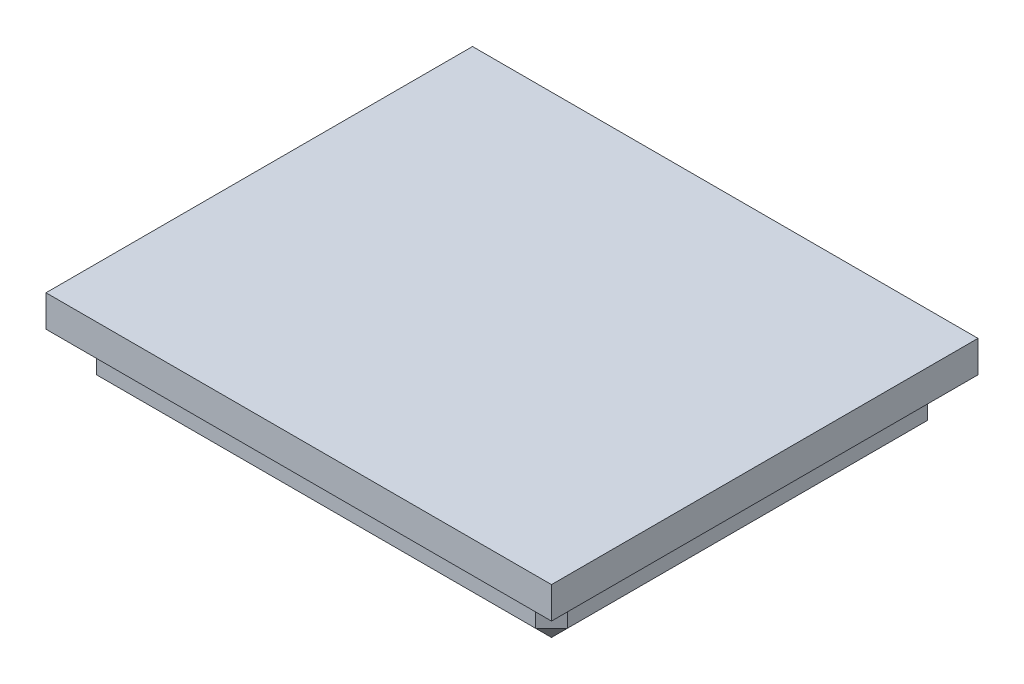
SolidWorks part; units mm, degrees
ref_plane "Спереди" through (0, 0, 0) normal (0, 0, 1) x (1, 0, 0)
ref_plane "Сверху" through (0, 0, 0) normal (0, 1, 0) x (1, 0, 0)
ref_plane "Справа" through (0, 0, 0) normal (1, 0, 0) x (0, 0, -1)
sketch "Sketch1" plane through (0, 0, 0) normal (0, 1, 0) x (1, 0, 0)
  line L1 (14.9, -12.4) -> (-14.9, -12.4)
  line L2 (14.9, -12.4) -> (14.9, 12.4)
  line L3 (14.9, 12.4) -> (-14.9, 12.4)
  line L4 (-14.9, -12.4) -> (-14.9, 12.4)
  line L5 (14.9, -12.4) -> (-14.9, 12.4) construction
  line L6 (14.9, 12.4) -> (-14.9, -12.4) construction
  point P0 (0, 0)
  dimension "D1" = 29.8
  dimension "D2" = 24.8
extrude "Boss-Extrude1" add sketch "Sketch1" along normal blind 3
sketch "Sketch2" plane through (0, 3, 0) normal (0, 1, 0) x (1, 0, 0)
  line L0 (-14.9, 12.4) -> (14.9, -12.4) construction
  line L1 (0, 13.5) -> (0, -13.5) construction
  line L2 (16, -13.5) -> (-16, -13.5)
  line L3 (16, -13.5) -> (16, 13.5)
  line L4 (16, 13.5) -> (-16, 13.5)
  line L5 (-16, -13.5) -> (-16, 13.5)
  line L6 (16, -13.5) -> (-16, 13.5) construction
  line L7 (16, 13.5) -> (-16, -13.5) construction
  point P4 (0, 0)
  dimension "D1" = 32
  dimension "D2" = 27
extrude "Boss-Extrude2" add sketch "Sketch2" along normal blind 2
chamfer "Chamfer1" distance 1 angle 45 8 edges at (-14.9, 0, 0) (0, 0, 12.4) (14.9, 0, 0) (0, 0, -12.4) (14.9, 1.5, 12.4) (-14.9, 1.5, 12.4) (-14.9, 1.5, -12.4) (14.9, 1.5, -12.4)
